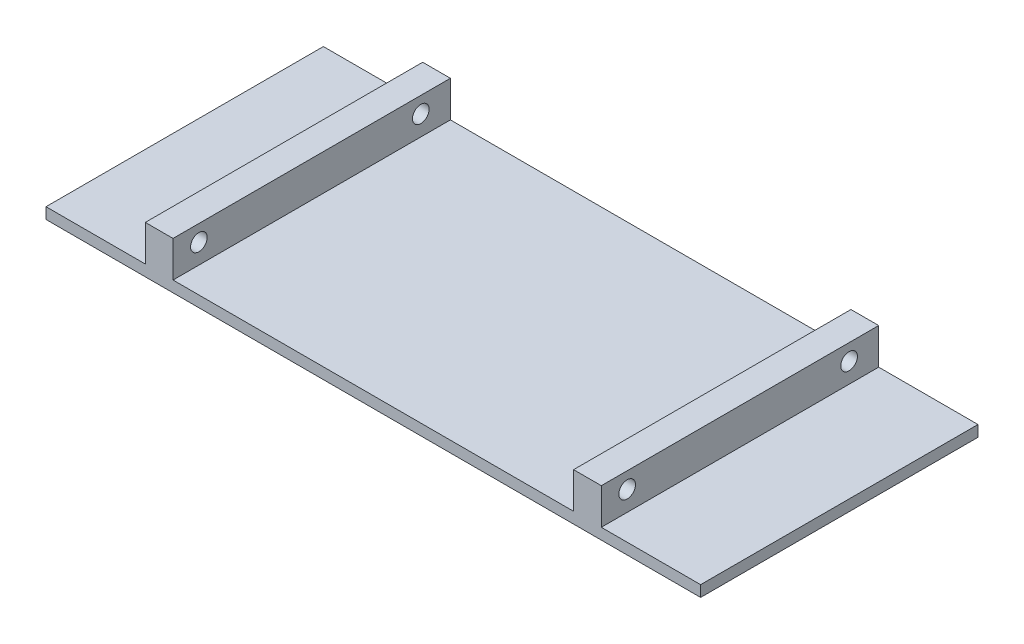
SolidWorks part; units mm, degrees
ref_plane "Front Plane" through (0, 0, 0) normal (0, 0, 1) x (1, 0, 0)
ref_plane "Top Plane" through (0, 0, 0) normal (0, 1, 0) x (1, 0, 0)
ref_plane "Right Plane" through (0, 0, 0) normal (1, 0, 0) x (0, 0, -1)
sketch "Sketch1" plane through (0, 0, 0) normal (0, 1, 0) x (1, 0, 0)
  line L1 (-59, 25) -> (59, 25)
  line L2 (-59, 25) -> (-59, -25)
  line L3 (-59, -25) -> (59, -25)
  line L4 (59, 25) -> (59, -25)
  line L5 (-59, 25) -> (59, -25) construction
  line L6 (-59, -25) -> (59, 25) construction
  point P0 (0, 0)
  dimension "D1" = 118
  dimension "D2" = 50
extrude "Boss-Extrude1" add sketch "Sketch1" along normal blind 2
sketch "Sketch2" plane through (0, 2, 0) normal (0, 1, 0) x (1, 0, 0)
  line L0 (-59, -25) -> (59, -25) construction
  line L1 (-41.1, -25) -> (-36.1, -25)
  line L2 (-41.1, -25) -> (-41.1, 25)
  line L3 (-41.1, 25) -> (-36.1, 25)
  line L4 (-36.1, -25) -> (-36.1, 25)
  line L5 (-59, 25) -> (-59, -25) construction
  line L7 (0, 0) -> (0, -25) construction
  line L10 (41.1, 25) -> (36.1, 25)
  line L11 (41.1, -25) -> (41.1, 25)
  line L12 (41.1, -25) -> (36.1, -25)
  line L13 (36.1, -25) -> (36.1, 25)
  dimension "D1" = 5
  dimension "D2" = 17.9
  dimension "D3" = 50
extrude "Boss-Extrude2" add sketch "Sketch2" along normal blind 6.5
sketch "Sketch3" plane through (-36.1, 0, 0) normal (1, 0, 0) x (0, 0, -1)
  line L0 (-25, 8.5) -> (-25, 2) construction
  line L1 (-25, 8.5) -> (25, 8.5) construction
  line L2 (25, 8.5) -> (25, 2) construction
  circle A4 centre (-20.34, 5.5898) radius 1.5
  circle A5 centre (19.66, 5.6) radius 1.5
  dimension "D1" = 3
  dimension "D2" = 2.9102
  dimension "D3" = 4.66
  dimension "D4" = 2.9
  dimension "D5" = 5.34
  dimension "D6" = 3
extrude "Cut-Extrude1" cut sketch "Sketch3" against normal blind 7
ref_plane "Plane1" through (0, 0, 0) normal (1, 0, 0) x (0, 0, -1)
mirror "Mirror1" about plane through (0, 0, 0) normal (1, 0, 0) of "Cut-Extrude1"
